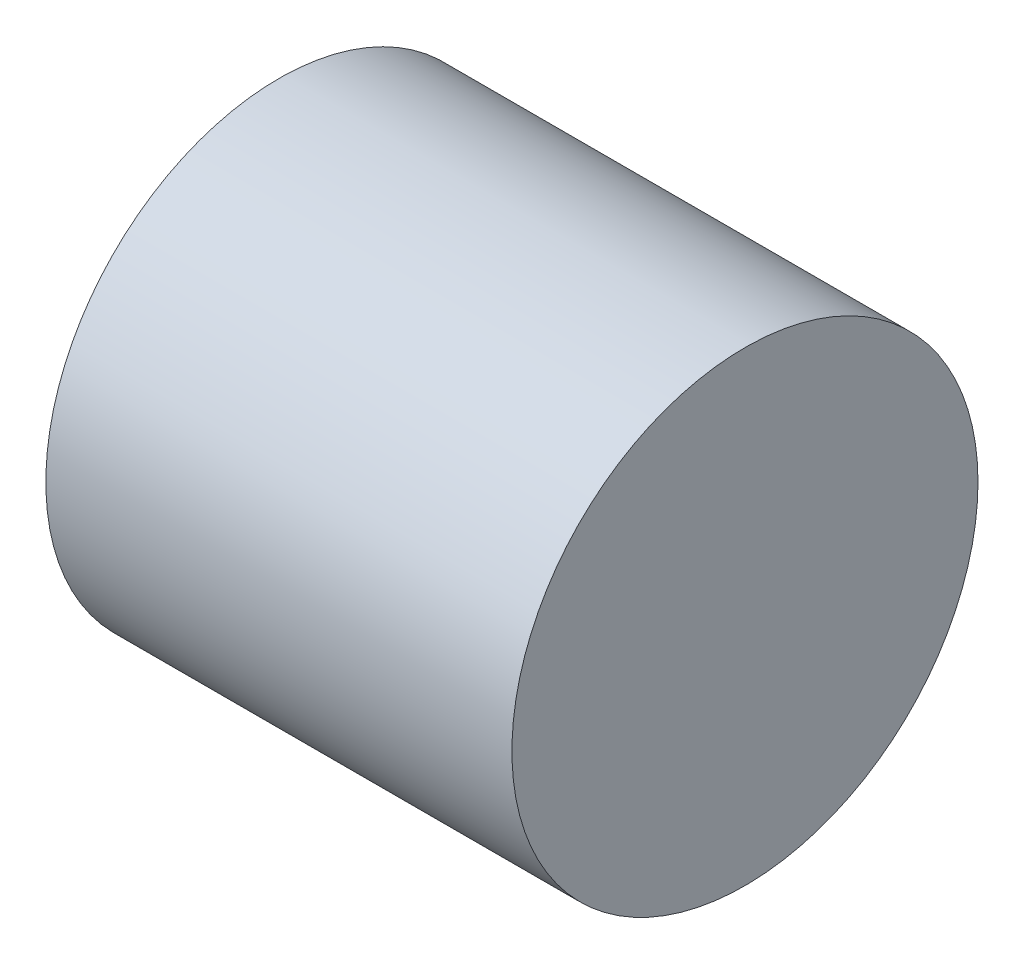
SolidWorks part; units mm, degrees
ref_plane "Ön Düzlem" through (0, 0, 0) normal (0, 0, 1) x (1, 0, 0)
ref_plane "Üst Düzlem" through (0, 0, 0) normal (0, 1, 0) x (1, 0, 0)
ref_plane "Sağ Düzlem" through (0, 0, 0) normal (1, 0, 0) x (0, 0, -1)
sketch "Sketch1" plane through (0, 0, 0) normal (1, 0, 0) x (0, 0, -1)
  circle A0 centre (0, 0) radius 10
extrude "Boss-Extrude1" add sketch "Sketch1" along normal blind 20
sketch "Sketch2" plane through (0, 0, 0) normal (-1, 0, 0) x (0, 0, 1)
  line L0 (-2.2361, 2) -> (2.2361, 2)
  arc A0 (-2.2361, 2) -> (2.2361, 2) centre (0, 0) ccw
  dimension "D1" = 2
  dimension "D2" = 3
extrude "Cut-Extrude1" cut sketch "Sketch2" against normal blind 10
